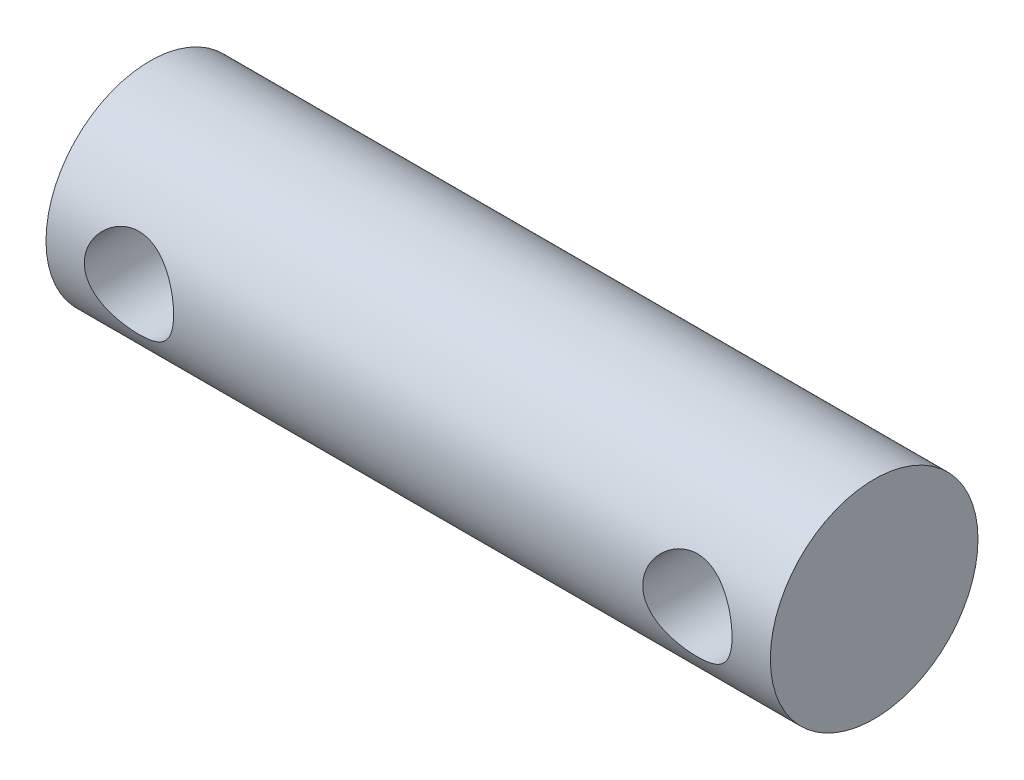
SolidWorks part; units mm, degrees
ref_plane "Front Plane" through (0, 0, 0) normal (0, 0, 1) x (1, 0, 0)
ref_plane "Top Plane" through (0, 0, 0) normal (0, 1, 0) x (1, 0, 0)
ref_plane "Right Plane" through (0, 0, 0) normal (1, 0, 0) x (0, 0, -1)
ref_plane "Plane1" through (32.0157, 0, 0) normal (1, 0, 0) x (0, 0, -1)
sketch "Sketch1" plane through (32.0157, 0, 0) normal (1, 0, 0) x (0, 0, -1)
  circle A0 centre (136.3281, 49.8362) radius 5
  point P3 (136.1778, 51.2476)
  point P6 (136.3281, 49.8362)
  dimension "D1" = 10
extrude "Boss-Extrude1" add sketch "Sketch1" along normal blind 23.71 and the other way blind 11.17
ref_plane "Plane2" through (0, 0, -131.3281) normal (0, 0, 1) x (1, 0, 0)
sketch "Sketch2" plane through (0, 0, -131.3281) normal (0, 0, 1) x (1, 0, 0)
  line L0 (55.7257, 49.8362) -> (20.8457, 49.8362) construction
  line L1 (55.7257, 44.8362) -> (55.7257, 54.8362) construction
  line L2 (20.8457, 54.8362) -> (20.8457, 44.8362) construction
  line L5 (47.7307, 57.4562) -> (47.7307, -52.26) construction
  line L6 (28.8407, 70.7912) -> (28.8407, 28.8812) construction
  circle A1 centre (51.7307, 49.8362) radius 2.15
  circle A2 centre (24.8408, 49.8362) radius 2.15
  point P10 (-52.5252, 49.8362)
  point P11 (-52.8084, 49.8362)
  point P12 (50.5292, 49.8362)
  dimension "D1" = 4.3
  dimension "D2" = 4.3
  dimension "D4" = 4
  dimension "D3" = 4
extrude "Cut-Extrude1" cut sketch "Sketch2" against normal through all
